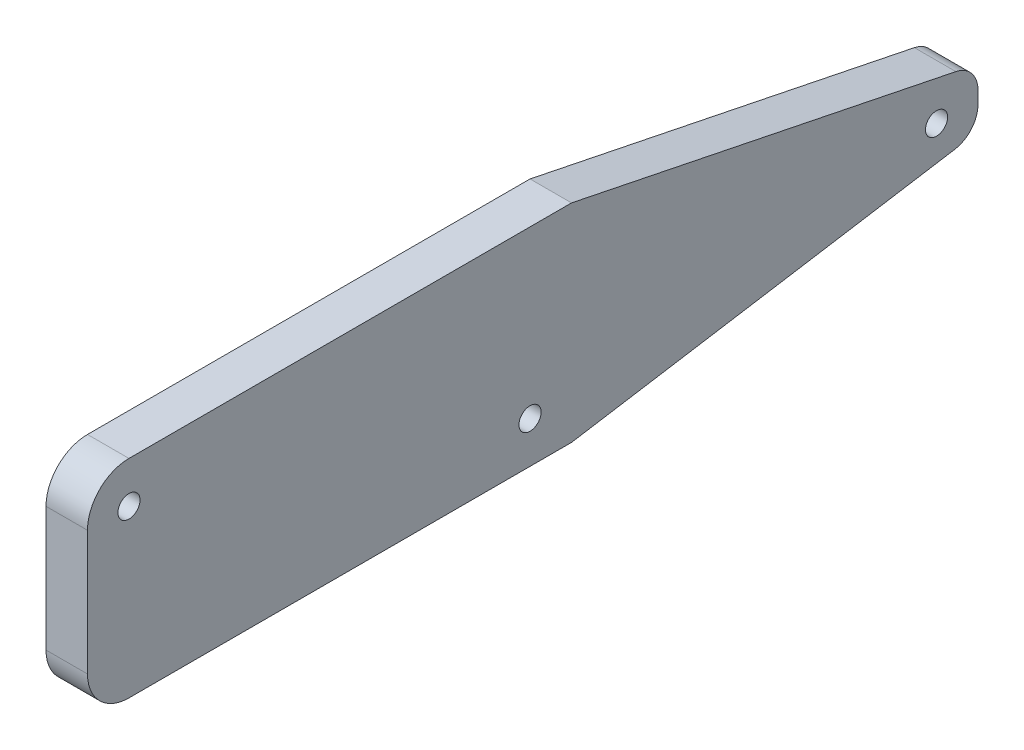
SolidWorks part; units mm, degrees
material "Teca"
ref_plane "Front Plane" through (0, 0, 0) normal (0, 0, 1) x (1, 0, 0)
ref_plane "Top Plane" through (0, 0, 0) normal (0, 1, 0) x (1, 0, 0)
ref_plane "Right Plane" through (0, 0, 0) normal (1, 0, 0) x (0, 0, -1)
sketch "Esboço1" plane through (0, 0, 0) normal (1, 0, 0) x (0, 0, -1)
  line L0 (-26.3179, 0) -> (-26.3179, 7.5)
  line L1 (-26.3179, 7.5) -> (8.6821, 7.5)
  line L4 (8.6821, -7.5) -> (-26.3179, -7.5)
  line L5 (-26.3179, -7.5) -> (-26.3179, 0)
  line L6 (-394.9557, 0) -> (19352.8294, 0) construction
  line L15 (8.6821, -992.5) -> (8.6821, 49007.5) construction
  line L16 (38.076, -1.0303) -> (38.076, -0.133)
  line L17 (8.6821, 7.5) -> (36.476, 1.8266)
  line L18 (8.6821, -7.5) -> (36.3962, -3.0045)
  arc A2 (36.3962, -3.0045) -> (38.076, -1.0303) centre (36.076, -1.0303) ccw
  arc A3 (38.076, -0.133) -> (36.476, 1.8266) centre (36.076, -0.133) ccw
  circle A4 centre (-23.3179, 4.5) radius 0.8
  circle A5 centre (5.6821, -4.5) radius 0.8
  circle A6 centre (35.076, -0.7196) radius 0.8
  point P14 (38.076, 1.5)
  dimension "D2" = 30
  dimension "D4" = 2
  dimension "D5" = 1.6
  dimension "D8" = 1.6
  dimension "D12" = 1.6
  dimension "D1" = 35
  dimension "D3" = 7.5
  dimension "D6" = 3
  dimension "D7" = 3
  dimension "D9" = 3
  dimension "D10" = 3
  dimension "D11" = 3
extrude "Ressalto-extrusão1" add sketch "Esboço1" along normal blind 3
fillet "Filete1" radius 3 1 edges at (1.5, -7.5, 26.3179)
fillet "Filete2" radius 3 1 edges at (1.5, 7.5, 26.3179)
